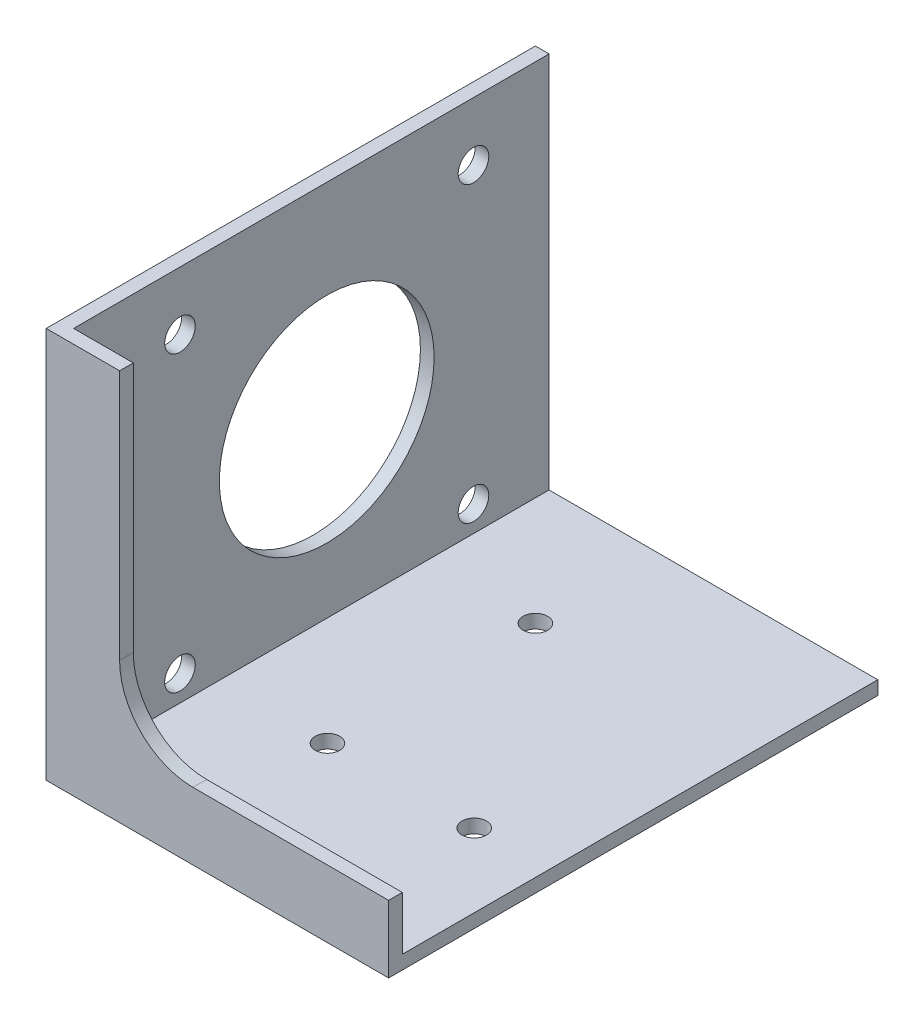
SolidWorks part; units mm, degrees
ref_plane "Front Plane" through (0, 0, 0) normal (0, 0, 1) x (1, 0, 0)
ref_plane "Top Plane" through (0, 0, 0) normal (0, 1, 0) x (1, 0, 0)
ref_plane "Right Plane" through (0, 0, 0) normal (1, 0, 0) x (0, 0, -1)
sketch "Sketch1" plane through (0, 0, 0) normal (0, 1, 0) x (1, 0, 0)
  line L1 (-17.78, 25.4) -> (17.78, 25.4)
  line L2 (-17.78, 25.4) -> (-17.78, -25.4)
  line L3 (-17.78, -25.4) -> (17.78, -25.4)
  line L4 (17.78, 25.4) -> (17.78, -25.4)
  point P4 (0, 0)
  point P5 (0, 0)
  point P6 (-17.78, 0)
  point P7 (0, 0)
  point P9 (0, 0)
  point P10 (0, 25.4)
  dimension "D1" = 35.56
  dimension "D2" = 50.8
extrude "Boss-Extrude1" add sketch "Sketch1" along normal mid plane 40.64
sketch "Sketch2" plane through (17.78, 0, 0) normal (1, 0, 0) x (0, 0, -1)
  line L3 (-23.9776, 20.32) -> (25.4, 20.32)
  line L4 (25.4, 20.32) -> (25.4, -18.8976)
  line L5 (-23.9776, -18.8976) -> (25.4, -18.8976)
  line L6 (-23.9776, 20.32) -> (-23.9776, -18.8976)
  line L7 (-23.9776, -18.8976) -> (25.4, -18.8976)
  line L8 (-23.9776, 20.32) -> (-23.9776, -18.8976)
  dimension "D1" = 1.4224
extrude "Cut-Extrude1" cut sketch "Sketch2" against normal offset from surface (34.1376 mm away) 1.4224 up to face at (-17.78, 0, 0)
sketch "Sketch3" plane through (0, -18.8976, 0) normal (0, 1, 0) x (1, 0, 0)
  line L0 (-16.3576, 25.4) -> (17.78, 25.4) construction
  line L1 (17.78, -23.9776) -> (17.78, 25.4) construction
  line L2 (-17.78, -25.4) -> (17.78, -25.4) construction
  circle A0 centre (-5.08, -8.89) radius 1.27
  circle A1 centre (10.16, -8.89) radius 1.27
  circle A2 centre (-5.08, 12.7) radius 1.27
  point P8 (0, 0)
  point P10 (0, 0)
  point P15 (0, 0)
  dimension "D1" = 2.54
  dimension "D2" = 12.7
  dimension "D3" = 7.62
  dimension "D4" = 15.24
  dimension "D5" = 16.51
extrude "Cut-Extrude2" cut sketch "Sketch3" against normal through all
sketch "Sketch6" plane through (0, 0, 23.9776) normal (0, 0, -1) x (-1, 0, 0)
  line L7 (-17.78, -20.32) -> (17.78, -20.32) construction
  line L8 (17.78, 20.32) -> (17.78, -20.32) construction
  line L9 (16.3576, 20.32) -> (-17.78, 20.32) construction
  line L10 (-17.78, -13.335) -> (-17.78, 20.32)
  line L11 (10.16, -5.715) -> (10.16, 20.32)
  line L16 (-17.78, -13.335) -> (2.54, -13.335)
  line L17 (-17.78, 20.32) -> (10.16, 20.32)
  arc A0 (10.16, -5.715) -> (2.54, -13.335) centre (2.54, -5.715) cw
  dimension "D3" = 7.62
  dimension "D1" = 6.985
  dimension "D2" = 7.62
extrude "Cut-Extrude3" cut sketch "Sketch6" against normal through all contours A0 L16 L10 L17 L11
sketch "Sketch7" plane through (-16.3576, 0, 0) normal (1, 0, 0) x (0, 0, -1)
  line L0 (-23.9776, 20.32) -> (25.4, 20.32) construction
  line L1 (-12.9286, -16.2306) -> (17.5514, -16.2306) construction
  line L2 (-12.9286, -16.2306) -> (-12.9286, 14.2494) construction
  line L3 (-12.9286, 14.2494) -> (17.5514, 14.2494) construction
  line L4 (17.5514, -16.2306) -> (17.5514, 14.2494) construction
  line L5 (-12.9286, -16.2306) -> (17.5514, 14.2494) construction
  line L6 (-12.9286, 14.2494) -> (17.5514, -16.2306) construction
  line L7 (25.4, 20.32) -> (25.4, -18.8976) construction
  circle A0 centre (2.3114, -0.9906) radius 11.1506
  circle A1 centre (-12.9286, 14.2494) radius 1.5875
  circle A2 centre (17.5514, 14.2494) radius 1.5875
  circle A3 centre (17.5514, -16.2306) radius 1.5875
  circle A4 centre (-12.9286, -16.2306) radius 1.5875
  point P6 (2.3114, 10.16)
  point P9 (13.462, -0.9906)
  dimension "D1" = 22.3012
  dimension "D5" = 3.175
  dimension "D2" = 30.48
  dimension "D3" = 10.16
  dimension "D4" = 11.938
extrude "Cut-Extrude4" cut sketch "Sketch7" against normal through all
